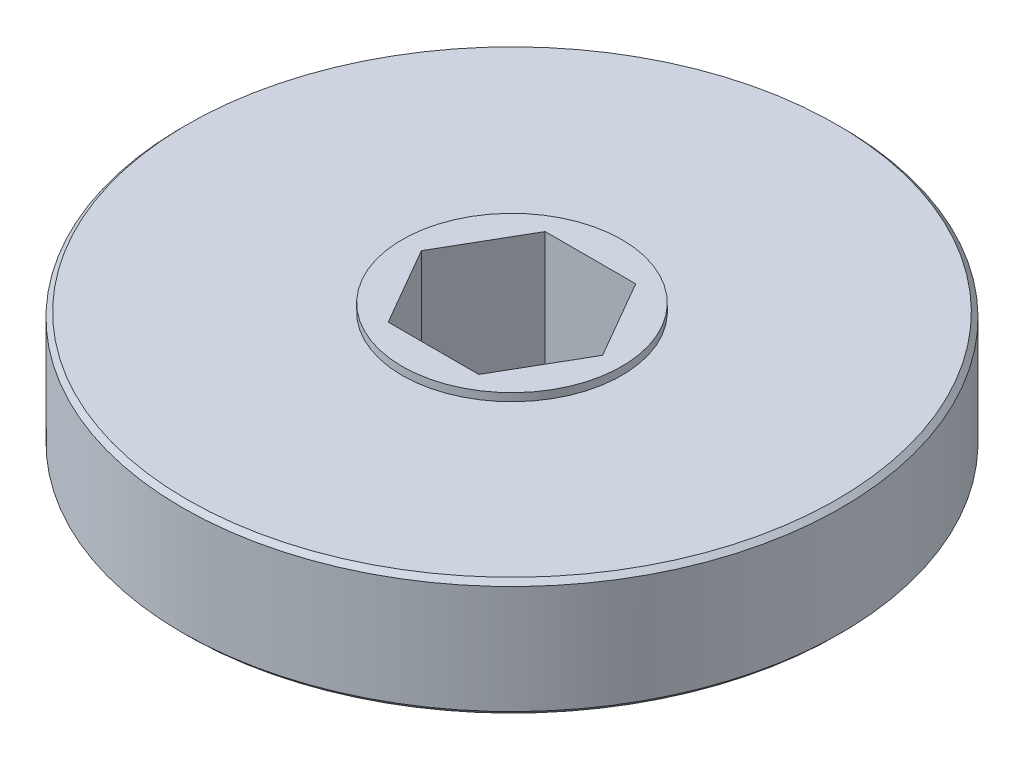
SolidWorks part; units mm, degrees
ref_plane "Front Plane" through (0, 0, 0) normal (0, 0, 1) x (1, 0, 0)
ref_plane "Top Plane" through (0, 0, 0) normal (0, 1, 0) x (1, 0, 0)
ref_plane "Right Plane" through (0, 0, 0) normal (1, 0, 0) x (0, 0, -1)
ref_plane "Plane1" through (0, 0, 0) normal (0, 0, -1) x (-1, 0, 0)
sketch "Sketch1" plane through (0, 0, 0) normal (0, 0, -1) x (-1, 0, 0)
  line L0 (-26.67, -10.16) -> (0, -10.16)
  line L1 (0, -10.16) -> (0, -0.635)
  line L2 (0, -0.635) -> (-26.67, -0.635)
  line L3 (-26.67, -0.635) -> (-26.67, -10.16)
  line L4 (0, -10.16) -> (0, -0.635) construction
revolve "Revolve1" add sketch "Sketch1" angle 360 about L4
sketch "Sketch2" plane through (0, -0.635, 0) normal (0, 1, 0) x (-1, 0, 0)
  circle A0 centre (0, 0) radius 8.89
extrude "Boss-Extrude1" add sketch "Sketch2" along normal blind 0.635
sketch "Sketch3" plane through (0, -10.16, 0) normal (0, -1, 0) x (1, 0, 0)
  line L0 (-7.3323, 0) -> (-3.6662, -6.35)
  line L1 (-3.6662, -6.35) -> (3.6662, -6.35)
  line L2 (3.6662, -6.35) -> (7.3323, 0)
  line L3 (7.3323, 0) -> (3.6662, 6.35)
  line L4 (3.6662, 6.35) -> (-3.6662, 6.35)
  line L5 (-3.6662, 6.35) -> (-7.3323, 0)
extrude "Cut-Extrude1" cut sketch "Sketch3" against normal through all
chamfer "Chamfer1" distance 0.381 angle 45 2 edges at (0, -10.16, 26.67) (0, -0.635, 26.67)
